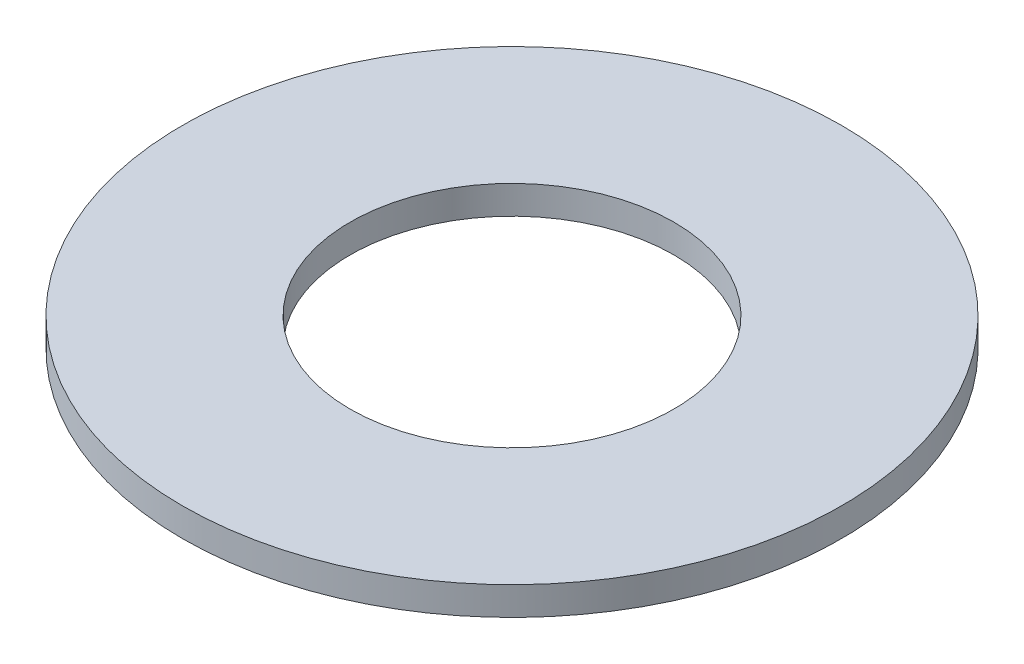
SolidWorks part; units mm, degrees
ref_plane "Front" through (0, 0, 0) normal (0, 0, 1) x (1, 0, 0)
ref_plane "Top" through (0, 0, 0) normal (0, 1, 0) x (1, 0, 0)
ref_plane "Right" through (0, 0, 0) normal (1, 0, 0) x (0, 0, -1)
sketch "Sketch1" plane through (0, 0, 0) normal (0, 1, 0) x (1, 0, 0)
  line L0 (0, 0) -> (5.8, 0) construction
  circle A0 centre (0, 0) radius 5.8
  circle A1 centre (0, 0) radius 2.85
  dimension "D1" = 11.6
  dimension "D2" = 5.7
extrude "Boss-Extrude2" add sketch "Sketch1" along normal blind 0.5
